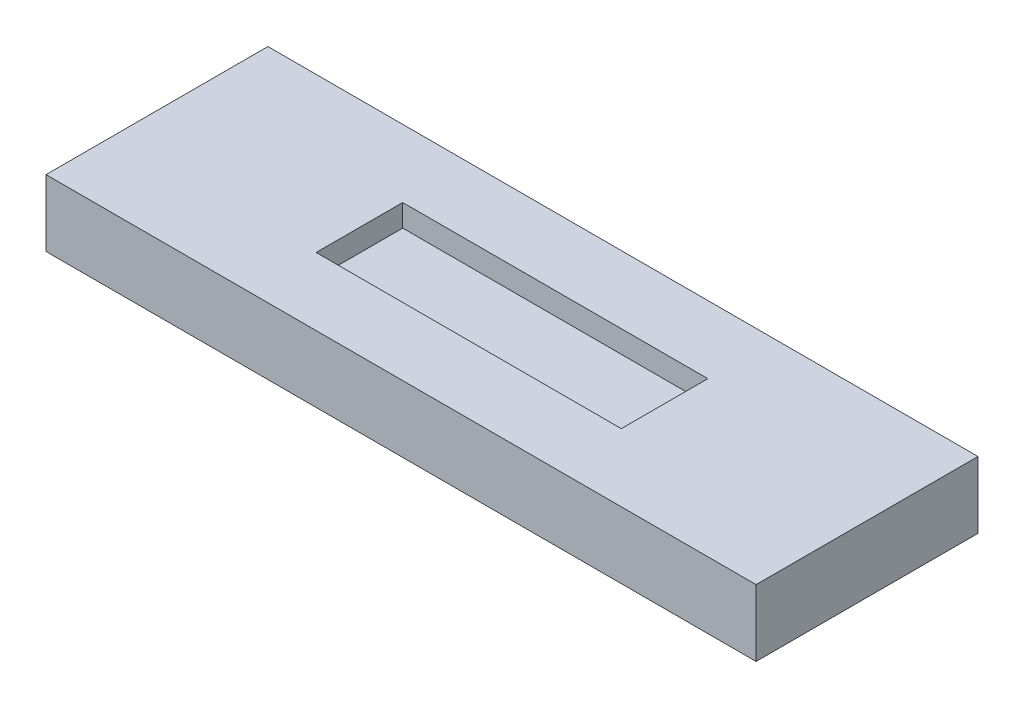
SolidWorks part; units mm, degrees
ref_plane "前基準面" through (0, 0, 0) normal (0, 0, 1) x (1, 0, 0)
ref_plane "上基準面" through (0, 0, 0) normal (0, 1, 0) x (1, 0, 0)
ref_plane "右基準面" through (0, 0, 0) normal (1, 0, 0) x (0, 0, -1)
sketch "草圖1" plane through (0, 0, 0) normal (0, 1, 0) x (1, 0, 0)
  line L1 (-16, -5) -> (16, -5)
  line L2 (-16, -5) -> (-16, 5)
  line L3 (-16, 5) -> (16, 5)
  line L4 (16, -5) -> (16, 5)
  line L5 (-16, -5) -> (16, 5) construction
  line L6 (-16, 5) -> (16, -5) construction
  point P0 (0, 0)
  dimension "D1" = 10
  dimension "D2" = 32
extrude "填料-伸長1" add sketch "草圖1" along normal blind 3
sketch "草圖2" plane through (0, 3, 0) normal (0, 1, 0) x (1, 0, 0)
  line L1 (-6.875, -1.95) -> (6.875, -1.95)
  line L2 (-6.875, -1.95) -> (-6.875, 1.95)
  line L3 (-6.875, 1.95) -> (6.875, 1.95)
  line L4 (6.875, -1.95) -> (6.875, 1.95)
  line L5 (-6.875, -1.95) -> (6.875, 1.95) construction
  line L6 (-6.875, 1.95) -> (6.875, -1.95) construction
  point P0 (0, 0)
  dimension "D1" = 3.9
  dimension "D2" = 13.75
extrude "除料-伸長1" cut sketch "草圖2" against normal blind 1
